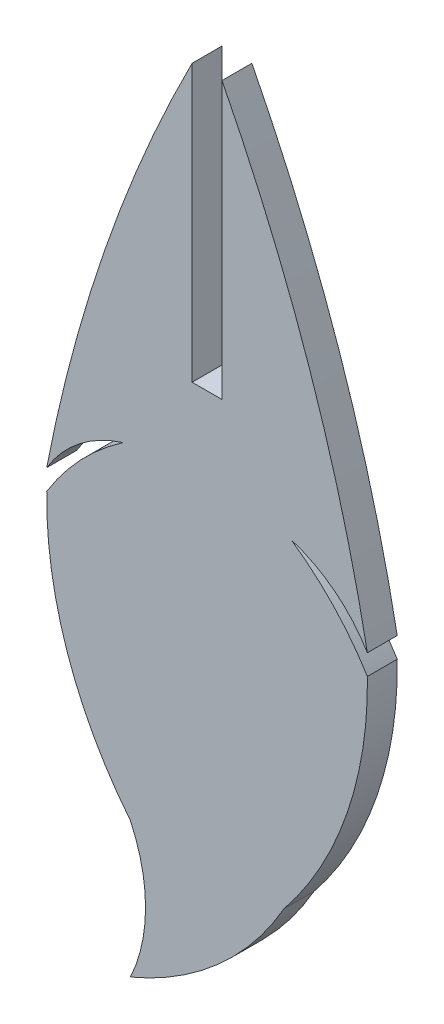
SolidWorks part; units mm, degrees
ref_plane "Front Plane" through (0, 0, 0) normal (0, 0, 1) x (1, 0, 0)
ref_plane "Top Plane" through (0, 0, 0) normal (0, 1, 0) x (1, 0, 0)
ref_plane "Right Plane" through (0, 0, 0) normal (1, 0, 0) x (0, 0, -1)
sketch "Sketch1" plane through (0, 0, 0) normal (0, 0, 1) x (1, 0, 0)
  line L0 (-1.524, -34.6762) -> (0, -34.6762)
  line L1 (0, -34.6762) -> (0, -20.5841)
  line L2 (-0.762, -34.6762) -> (-0.762, -15.1233) construction
  line L3 (-1.524, -20.5841) -> (-1.524, -34.6762)
  arc A0 (0, -20.5841) -> (7.416, -42.1582) centre (-71.9693, -57.3849) cw
  arc A1 (7.416, -42.1582) -> (3.5271, -39.1056) centre (1.4811, -45.7156) ccw
  arc A2 (3.5271, -39.1056) -> (7.416, -43.2036) centre (-4.2086, -50.3408) cw
  arc A3 (7.416, -43.2036) -> (3.1505, -55.6111) centre (-11.8403, -43.5206) cw
  arc A4 (-8.94, -43.2036) -> (-4.6745, -55.6111) centre (10.3163, -43.5206) ccw
  arc A5 (-5.0511, -39.1056) -> (-8.94, -43.2036) centre (2.6846, -50.3408) ccw
  arc A6 (-8.94, -42.1582) -> (-5.0511, -39.1056) centre (-3.0051, -45.7156) cw
  arc A7 (-1.524, -20.5841) -> (-8.94, -42.1582) centre (70.4453, -57.3849) ccw
  arc A8 (-4.6745, -55.6111) -> (-4.6745, -62.5286) centre (-12.0071, -59.0699) cw
  arc A9 (-4.6745, -62.5286) -> (3.1505, -55.6111) centre (-10.9166, -47.5829) ccw
extrude "Boss-Extrude1" add sketch "Sketch1" along normal blind 1.524
